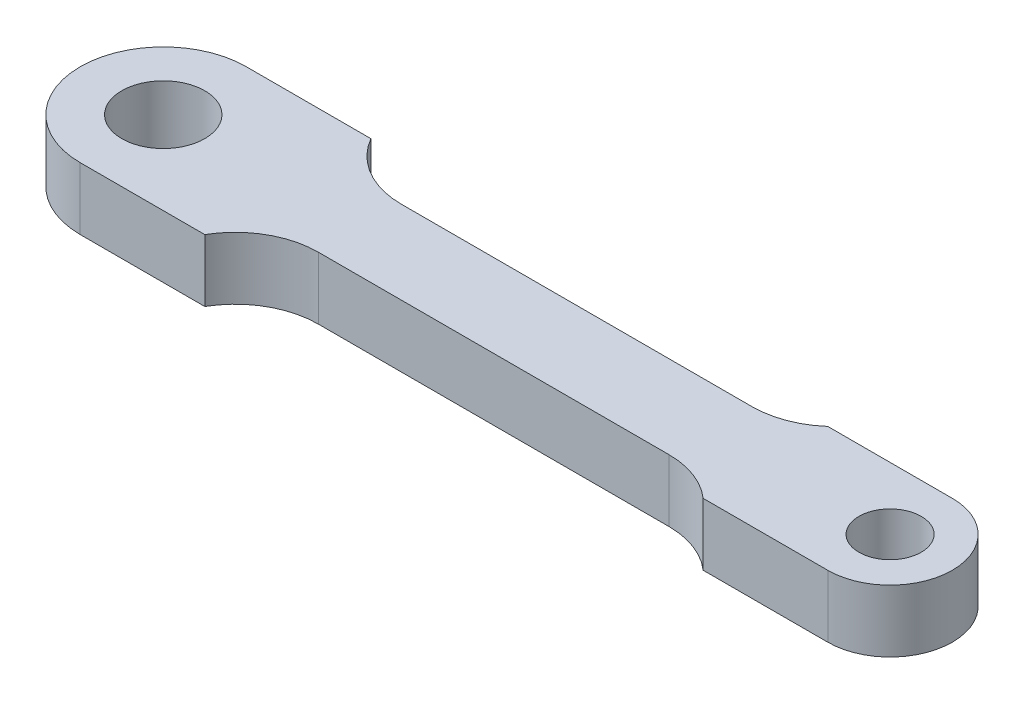
SolidWorks part; units mm, degrees
ref_plane "Front Plane" through (0, 0, 0) normal (0, 0, 1) x (1, 0, 0)
ref_plane "Top Plane" through (0, 0, 0) normal (0, 1, 0) x (1, 0, 0)
ref_plane "Right Plane" through (0, 0, 0) normal (1, 0, 0) x (0, 0, -1)
sketch "Sketch1" plane through (0, 0, 0) normal (0, 1, 0) x (1, 0, 0)
  line L0 (-10.5196, 4) -> (-4.5196, 4)
  line L1 (-10.5196, -4) -> (-4.5196, -4)
  line L2 (24.4804, -3) -> (18.4804, -3)
  line L3 (24.4804, 3) -> (18.4804, 3)
  line L4 (-1.0555, 2) -> (15.8346, 2)
  line L5 (-2.8484, 0) -> (18.9022, 0) construction
  line L6 (-1.0555, -2) -> (15.8346, -2)
  circle A0 centre (-10.5196, 0) radius 2
  circle A1 centre (24.4804, 0) radius 1.5
  arc A2 (-10.5196, 4) -> (-10.5196, -4) centre (-10.5196, 0) ccw
  arc A3 (24.4804, -3) -> (24.4804, 3) centre (24.4804, 0) ccw
  arc A4 (-4.5196, 4) -> (-1.0555, 2) centre (-1.0555, 6) ccw
  arc A5 (15.8346, 2) -> (18.4804, 3) centre (15.8346, 6) ccw
  arc A6 (15.8346, -2) -> (18.4804, -3) centre (15.8346, -6) cw
  arc A7 (-4.5196, -4) -> (-1.0555, -2) centre (-1.0555, -6) cw
  dimension "D1" = 6
  dimension "D2" = 3
  dimension "D3" = 8
  dimension "D4" = 4
  dimension "D9" = 8
  dimension "D5" = 6
  dimension "D6" = 35
  dimension "D7" = 2
extrude "Boss-Extrude1" add sketch "Sketch1" along normal mid plane 3
